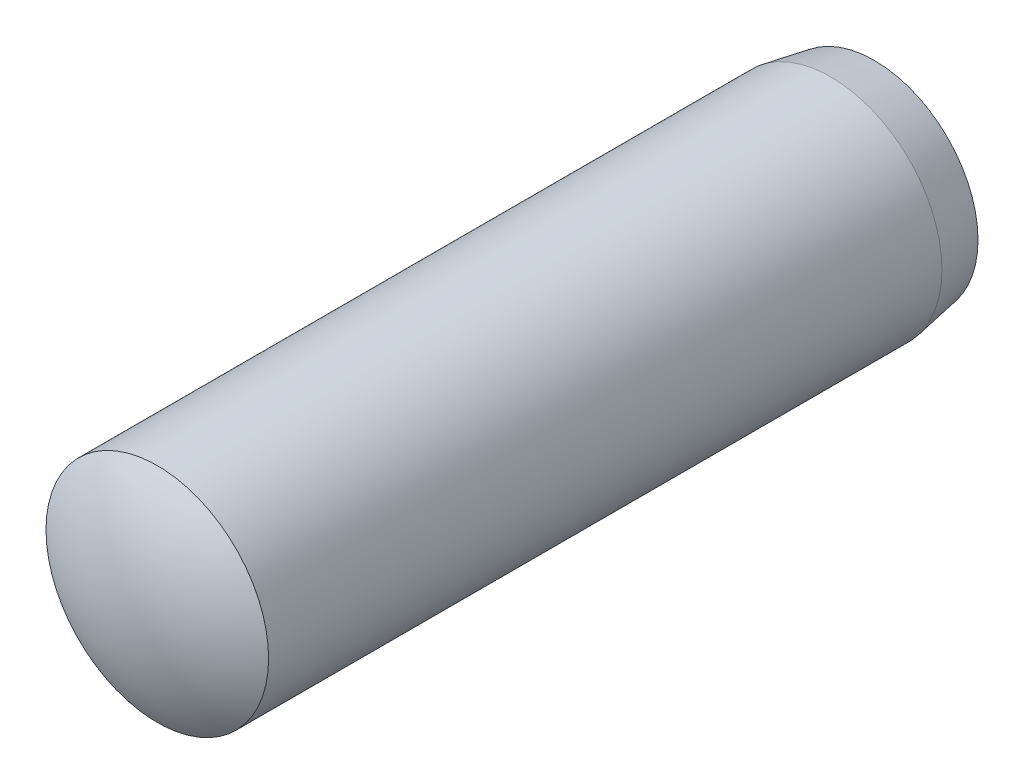
SolidWorks part; units mm, degrees
ref_plane "Vorne" through (0, 0, 0) normal (0, 0, 1) x (1, 0, 0)
ref_plane "Oben" through (0, 0, 0) normal (0, 1, 0) x (1, 0, 0)
ref_plane "Rechts" through (0, 0, 0) normal (1, 0, 0) x (0, 0, -1)
sketch "Skizze1" plane through (0, 0, 0) normal (0, 1, 0) x (1, 0, 0)
  line L0 (0, 14) -> (0, -14)
  line L1 (-4, 11.4) -> (-4, -12.8)
  line L2 (-4, 11.4) -> (-3.7224, 12.9742)
  arc A0 (0, 14) -> (-3.7224, 12.9742) centre (0, 6.7333) ccw
  arc A1 (0, -14) -> (-4, -12.8) centre (0, -6.7333) cw
  dimension "D4" = 1.2
  dimension "D1" = 28
  dimension "D2" = 4
  dimension "D3" = 10
  dimension "D5" = 2.6
revolve "Rotation1" add sketch "Skizze1" angle 360 about L0
